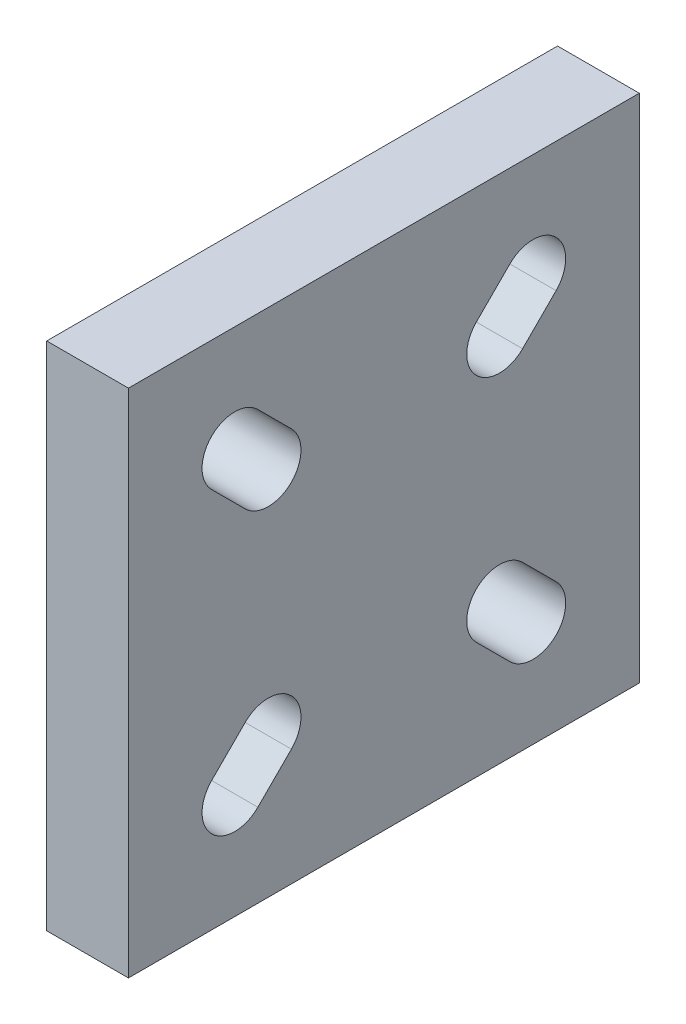
SolidWorks part; units mm, degrees
ref_plane "Front Plane" through (0, 0, 0) normal (0, 0, 1) x (1, 0, 0)
ref_plane "Top Plane" through (0, 0, 0) normal (0, 1, 0) x (1, 0, 0)
ref_plane "Right Plane" through (0, 0, 0) normal (1, 0, 0) x (0, 0, -1)
sketch "Sketch2" plane through (0, 0, 0) normal (1, 0, 0) x (0, 0, -1)
  line L1 (-12.5, -12.5) -> (12.5, -12.5)
  line L2 (-12.5, -12.5) -> (-12.5, 12.5)
  line L3 (-12.5, 12.5) -> (12.5, 12.5)
  line L4 (12.5, -12.5) -> (12.5, 12.5)
  line L5 (-12.5, -12.5) -> (4.5255, 4.5255) construction
  line L6 (-12.5, 12.5) -> (12.5, -12.5) construction
  line L8 (6.1661, 8.4288) -> (4.5255, 6.7882)
  line L11 (8.4288, 6.1661) -> (6.7882, 4.5255)
  line L12 (0, 0) -> (4.5255, 4.5255) construction
  line L13 (0, 0) -> (12.5, -12.5) construction
  line L14 (0, 0) -> (-12.5, -12.5) construction
  line L15 (0, 0) -> (-12.5, 12.5) construction
  line L16 (8.4288, 8.4288) -> (12.5, 12.5) construction
  line L17 (8.4288, 8.4288) -> (12.5, 12.5) construction
  line L18 (-12.5, 0) -> (12.5, 0) construction
  line L19 (0, 12.5) -> (0, -12.5) construction
  line L20 (8.4288, -6.1661) -> (6.7882, -4.5255)
  line L21 (6.1661, -8.4288) -> (4.5255, -6.7882)
  line L22 (-6.1661, -8.4288) -> (-4.5255, -6.7882)
  line L23 (-8.4288, -6.1661) -> (-6.7882, -4.5255)
  line L24 (-8.4288, 6.1661) -> (-6.7882, 4.5255)
  line L25 (-6.1661, 8.4288) -> (-4.5255, 6.7882)
  arc A0 (4.418, 6.6694) -> (6.6694, 4.418) centre (0, 0) ccw construction
  arc A1 (6.0818, 8.3377) -> (8.3377, 6.0818) centre (0, 0) ccw construction
  arc A2 (8.3377, 6.0818) -> (6.0818, 8.3377) centre (7.2974, 7.2974) ccw
  arc A3 (4.5255, 6.7882) -> (6.7882, 4.5255) centre (5.6569, 5.6569) ccw
  arc A4 (6.0818, -8.3377) -> (8.3377, -6.0818) centre (7.2974, -7.2974) ccw
  arc A5 (6.7882, -4.5255) -> (4.5255, -6.7882) centre (5.6569, -5.6569) ccw
  arc A6 (-8.3377, -6.0818) -> (-6.0818, -8.3377) centre (-7.2974, -7.2974) ccw
  arc A7 (-4.5255, -6.7882) -> (-6.7882, -4.5255) centre (-5.6569, -5.6569) ccw
  arc A8 (-6.0818, 8.3377) -> (-8.3377, 6.0818) centre (-7.2974, 7.2974) ccw
  arc A9 (-6.7882, 4.5255) -> (-4.5255, 6.7882) centre (-5.6569, 5.6569) ccw
  point P0 (0, 0)
  point P7 (13.4658, 8.4469)
  point P8 (7.2974, 7.2974)
  point P9 (-7.2974, 7.2974)
  point P10 (-7.2974, -7.2974)
  point P13 (7.2974, -7.2974)
  point P14 (-5.6569, 5.6569)
  point P15 (5.6569, 5.6569)
  point P16 (5.6569, -5.6569)
  point P17 (-5.6569, -5.6569)
  point P30 (0, 0)
  point P34 (0, 0)
  point P61 (0, 0)
  dimension "D1" = 3.2
  dimension "D2" = 20.6403
  dimension "D3" = 16
  dimension "D4" = 3.2
  dimension "D5" = 25
  dimension "D6" = 25
  dimension "D7" = 4
extrude "Boss-Extrude1" add sketch "Sketch2" along normal blind 4 contours L1 L4 L3 L2 A9 L24 A8 L25 A7 L22 A6 L23 A5 L20 A4 L21 A3 L8 A2 L11
